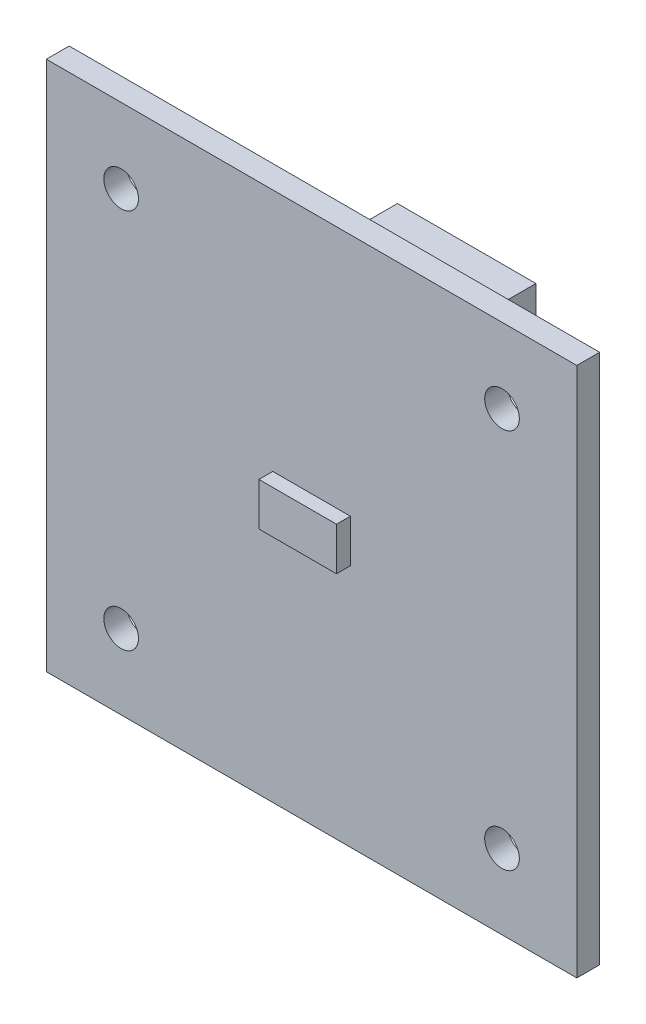
SolidWorks part; units mm, degrees
ref_plane "Front" through (0, 0, 0) normal (0, 0, 1) x (1, 0, 0)
ref_plane "Top" through (0, 0, 0) normal (0, 1, 0) x (1, 0, 0)
ref_plane "Right" through (0, 0, 0) normal (1, 0, 0) x (0, 0, -1)
sketch "Skizze1" plane through (0, 0, 0) normal (0, 0, 1) x (1, 0, 0)
  line L1 (-19.15, -19.15) -> (19.15, -19.15)
  line L2 (-19.15, -19.15) -> (-19.15, 19.15)
  line L3 (-19.15, 19.15) -> (19.15, 19.15)
  line L4 (19.15, -19.15) -> (19.15, 19.15)
  line L5 (-19.15, -19.15) -> (19.15, 19.15) construction
  line L6 (-19.15, 19.15) -> (19.15, -19.15) construction
  circle A0 centre (-13.75, 13.75) radius 1.25
  circle A1 centre (13.75, 13.75) radius 1.25
  circle A2 centre (13.75, -13.75) radius 1.25
  circle A3 centre (-13.75, -13.75) radius 1.25
  point P0 (0, 0)
  dimension "D3" = 2.5
  dimension "D1" = 38.3
  dimension "D2" = 27.5
extrude "Aufsatz-Linear austragen1" add sketch "Skizze1" along normal blind 1.65
sketch "Skizze2" plane through (0, 0, 1.65) normal (0, 0, 1) x (1, 0, 0)
  line L1 (-2.8, -1.55) -> (2.8, -1.55)
  line L2 (-2.8, -1.55) -> (-2.8, 1.55)
  line L3 (-2.8, 1.55) -> (2.8, 1.55)
  line L4 (2.8, -1.55) -> (2.8, 1.55)
  line L5 (-2.8, -1.55) -> (2.8, 1.55) construction
  line L6 (-2.8, 1.55) -> (2.8, -1.55) construction
  point P0 (0, 0)
  dimension "D1" = 5.6
  dimension "D2" = 3.1
extrude "Aufsatz-Linear austragen2" add sketch "Skizze2" along normal blind 1
sketch "Sketch1" plane through (0, 0, 1.65) normal (0, 0, 1) x (1, 0, 0)
  circle A0 centre (0, 0) radius 5
  dimension "D1" = 10
sketch "Sketch2" plane through (0, 0, 0) normal (0, 0, -1) x (-1, 0, 0)
  line L0 (-19.15, 19.15) -> (19.15, 19.15) construction
  line L1 (-8.55, 10.45) -> (1.45, 10.45)
  line L2 (-8.55, 10.45) -> (-8.55, 15.15)
  line L3 (-8.55, 15.15) -> (1.45, 15.15)
  line L4 (1.45, 10.45) -> (1.45, 15.15)
  line L5 (-19.15, -19.15) -> (-19.15, 19.15) construction
  dimension "D1" = 10
  dimension "D2" = 4.7
  dimension "D3" = 4
  dimension "D4" = 10.6
extrude "Boss-Extrude1" add sketch "Sketch2" along normal blind 6
